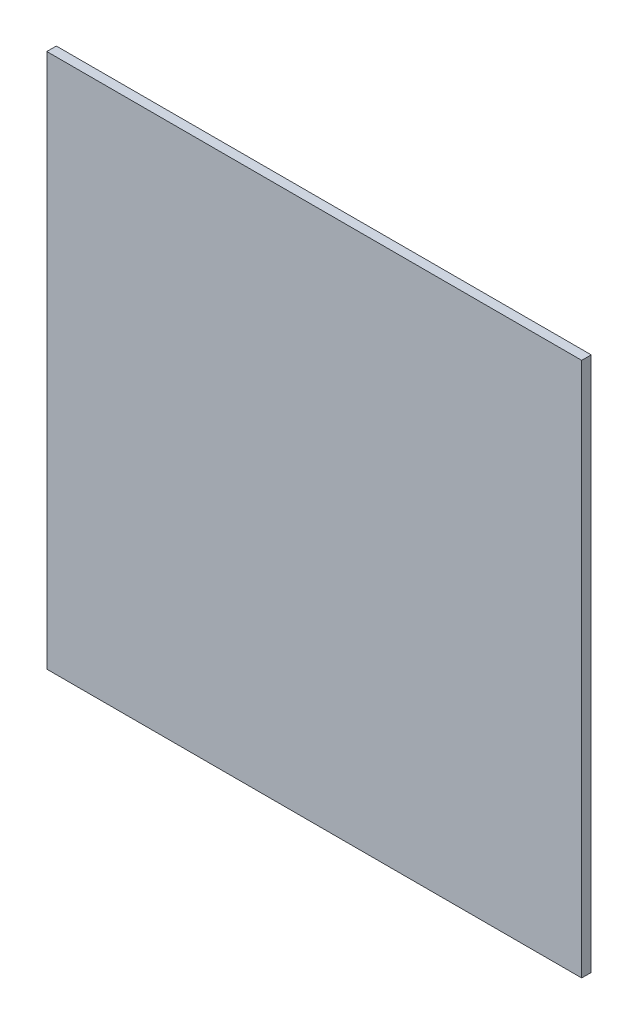
SolidWorks part; units mm, degrees
ref_plane "Ebene vorne" through (0, 0, 0) normal (0, 0, 1) x (1, 0, 0)
ref_plane "Ebene oben" through (0, 0, 0) normal (0, 1, 0) x (1, 0, 0)
ref_plane "Ebene rechts" through (0, 0, 0) normal (1, 0, 0) x (0, 0, -1)
sketch "Skizze1" plane through (0, 0, 0) normal (0, 0, 1) x (1, 0, 0)
  line L1 (-225, -225) -> (225, -225)
  line L2 (-225, -225) -> (-225, 225)
  line L3 (-225, 225) -> (225, 225)
  line L4 (225, -225) -> (225, 225)
  line L5 (-225, -225) -> (225, 225) construction
  line L6 (-225, 225) -> (225, -225) construction
  point P0 (0, 0)
  dimension "D1" = 450
  dimension "D2" = 450
extrude "Aufsatz-Linear austragen1" add sketch "Skizze1" along normal blind 8
